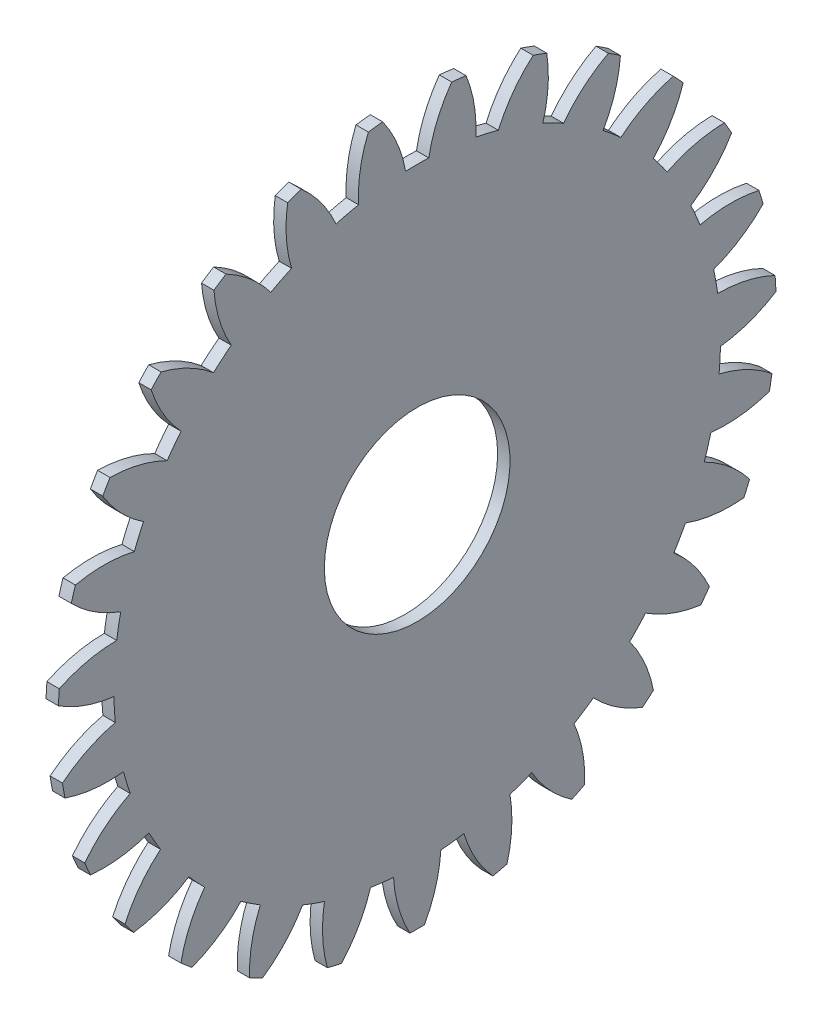
SolidWorks part; units mm, degrees
ref_plane "Plane1" through (0, 0, 0) normal (0, 0, 1) x (1, 0, 0)
ref_plane "Plane2" through (0, 0, 0) normal (0, 1, 0) x (1, 0, 0)
ref_plane "Plane3" through (0, 0, 0) normal (1, 0, 0) x (0, 0, -1)
other "Configuration Table"
sketch "HoldingSke" plane through (0, 0, 0) normal (0, 1, 0) x (1, 0, 0)
  line L0 (0, 0) -> (0.1485, -0.0757)
  line L1 (-15, 0) -> (100, 0) construction
  line L2 (0, 0) -> (-2.1039, 2.3779)
  line L3 (0, 0) -> (-11.863, 4.5341)
  line L4 (0, 0) -> (7.6947, 3.9207)
  line L5 (0, 0) -> (-46.8476, -17.4728)
  line L6 (0, 0) -> (-2.4869, -1.6779)
  line L7 (-2.1039, 2.3779) -> (8.6586, 51.2059)
  line L8 (-76.2, 54.61) -> (-72.4, 54.61)
  line L9 (-71.009, 38.7566) -> (-53.1078, 45.2721)
  line L10 (-76.2, 71.12) -> (104.1128, 71.12)
  line L11 (0, 0) -> (-3, 0)
  line L12 (-76.2, 101.6) -> (-75.993, 101.6)
  line L13 (24.9733, 27.94) -> (52.9518, 28.4284)
  line L14 (24.9733, 27.94) -> (24.9743, 27.94)
  line L15 (24.9733, 27.94) -> (100.4006, 29.5858)
  line L16 (-63.627, -6) -> (-12.827, -6)
  circle A0 centre (0, 0) radius 22.5
  circle A1 centre (0, 0) radius 37.5
  circle A2 centre (0, 0) radius 37.5
  circle A3 centre (0, 0) radius 22.5
  dimension "MHD" = 75
  dimension "Hub_dia" = 75
  dimension "Bore" = 45
  dimension "MBD" = 45
  dimension "Num_teeth" = 27
  dimension "Pitch" = 0.1667
  dimension "Overall_len" = 50
  dimension "Show_teeth" = 27
  dimension "Thickness" = 3
  dimension "OAL" = 50.0001
  dimension "T_dim" = 3.8
  dimension "Ap" = 20
  dimension "H" = 19.05
  dimension "Pitch_radius" = 180.3128
  dimension "Width" = 3
  dimension "Backlash" = 0.207
  dimension "Addendum_fac" = 1
  dimension "Dedendum_fac" = 1.25
  dimension "Clearance_fac" = 0.25
  dimension "Dedendum_add" = 0.001
  dimension "Module" = 6
sketch "BasProSke" plane through (0, 0, 0) normal (0, 1, 0) x (1, 0, 0)
  line L0 (-10, 0) -> (60, 0) construction
  line L1 (0, 0) -> (0, 87)
  line L2 (0, 0) -> (3, 0)
  line L3 (3, 0) -> (3, 87)
  line L4 (3, 87) -> (0, 87)
  dimension "Thickness" = 3
  dimension "Diameter" = 174
revolve "Base-Revolve" add sketch "BasProSke" angle 360 about L0
sketch "TooCutSke" plane through (0, 0, 0) normal (1, 0, 0) x (0, 0, -1)
  line L1 (0, 0) -> (0, 107) construction
  line L2 (0, 0) -> (-5.0719, 80.8411) construction
  line L3 (0, 0) -> (-18.7799, 160.6727) construction
  line L4 (-5.0719, 80.8411) -> (-9.39, 80.3363) construction
  arc A0 (2.8118, 73.4452) -> (-2.8118, 73.4452) centre (0, 0) ccw
  arc A1 (8.3748, 86.6215) -> (-8.3748, 86.6215) centre (0, 0) ccw
  circle A2 centre (0, 0) radius 81 construction
  circle A3 centre (0, 0) radius 76.1151 construction
  arc A4 (-2.8118, 73.4452) -> (-8.3748, 86.6215) centre (-34.706, 67.7422) ccw
  arc A5 (8.3748, 86.6215) -> (2.8118, 73.4452) centre (34.706, 67.7422) ccw
  dimension "Root_dia" = 146.998
  dimension "Overcut_dia" = 174.0508
  dimension "Pitch_dia" = 162
  dimension "Base_dia" = 152.2302
  dimension "Flank_rad" = 32.4
  dimension "Half_ang" = 6.667
  dimension "Half_CT" = 4.3475
extrude "ToothCut" cut sketch "TooCutSke" along normal through all
fillet "Breaks" [suppressed] radius 0.12
fillet "RootFillets" [suppressed] radius 1.501
pattern_circular "TeethCuts" count 27 every 13.333 about axis through (-10, 0, 0) along (1, 0, 0) of "ToothCut", "RootFillets", "Breaks"
sketch "HubNeaOneSke" plane through (0, 0, 0) normal (-1, 0, 0) x (0, 0, 1)
  circle A0 centre (0, 0) radius 37.5
  dimension "Diameter" = 75
extrude "HubNearOne" [suppressed] add sketch "HubNeaOneSke" along normal blind 47.0001
sketch "HubNeaBotSke" plane through (0, 0, 0) normal (-1, 0, 0) x (0, 0, 1)
  circle A0 centre (0, 0) radius 37.5
  dimension "Diameter" = 75
extrude "HubNearBoth" [suppressed] add sketch "HubNeaBotSke" along normal blind 23.5
ref_plane "FarPln" through (3, 0, 0) normal (1, 0, 0) x (0, 0, -1)
sketch "HubFarSke" plane through (3, 0, 0) normal (1, 0, 0) x (0, 0, -1)
  circle A0 centre (0, 0) radius 37.5
  dimension "Diameter" = 75
extrude "HubFar" [suppressed] add sketch "HubFarSke" along normal blind 23.5
sketch "BorSke" plane through (0, 0, 0) normal (1, 0, 0) x (0, 0, -1)
  circle A0 centre (0, 0) radius 22.5
  dimension "Diameter" = 45
extrude "Bore" cut sketch "BorSke" along normal mid plane 100.0001
sketch "KeySke" plane through (0, 0, 0) normal (1, 0, 0) x (0, 0, -1)
  line L0 (-7, 0) -> (-7, 26.3)
  line L1 (-7, 26.3) -> (7, 26.3)
  line L2 (7, 26.3) -> (7, 0)
  line L3 (0, 0) -> (0, 34) construction
  line L4 (-7, 0) -> (7, 0)
  dimension "Offset" = 26.3
  dimension "Width" = 14
extrude "Keyway" [suppressed] cut sketch "KeySke" along normal mid plane 100.0001
pattern_circular "Keyway2" [suppressed] count 2 every 90 about axis through (-10, 0, 0) along (1, 0, 0)
sketch "Sketch1" plane through (3, 0, 0) normal (1, 0, 0) x (0, 0, -1)
  circle A0 centre (0, 0) radius 81.1117
equation "' \"Module@HoldingSke\" = 6.35"
equation "' \"Num_teeth@HoldingSke\" = 12"
equation "' \"Ap@HoldingSke\" =  20"
equation "' \"Ap@HoldingSke\" = 20"
equation "' \"Width@HoldingSke\" = 0.5 * 25.4"
equation "' \"Hub_dia@HoldingSke\"= 1 * 25.4"
equation "' \"Hub_dia@HoldingSke\" = 1 * 25.4"
equation "' \"Overall_len@HoldingSke\" = 1.0 * 25.4"
equation "' \"Bore@HoldingSke\" = 0.75 * 25.4"
equation "' \"T_dim@HoldingSke\" = 0.1 * 25.4"
equation "' \"Width@KeySke\" = 0.25 * 25.4"
equation "' \"Show_teeth@HoldingSke\" = 13"
equation "' \"Backlash@HoldingSke\" = 0.009 * 25.4"
equation "' \"Addendum_fac@HoldingSke\" = 1.0"
equation "' \"Dedendum_fac@HoldingSke\" = 1.25"
equation "' \"Dedendum_add@HoldingSke\" = 0.00005 * 25.4"
equation "' \"Clearance_fac@HoldingSke\" = 0.25"
equation "\"Pitch@HoldingSke\" = 1 / \"Module@HoldingSke\""
equation "\"Overcut_dia@TooCutSke\" = (\"Num_teeth@HoldingSke\" + 2 * \"Addendum_fac@HoldingSke\") / \"Pitch@HoldingSke\" + 0.002 * 25.4"
equation "\"Pitch_dia@TooCutSke\" = \"Num_teeth@HoldingSke\" / \"Pitch@HoldingSke\""
equation "\"Base_dia@TooCutSke\" = \"Num_teeth@HoldingSke\" / \"Pitch@HoldingSke\" * cos((\"Ap@HoldingSke\"  * 3.14159265 / 180))"
equation "\"Root_dia@TooCutSke\" = (\"Num_teeth@HoldingSke\" + 2) / \"Pitch@HoldingSke\" - 2 * (\"Addendum_fac@HoldingSke\" + \"Dedendum_fac@HoldingSke\") / \"Pitch@HoldingSke\" - \"Dedendum_add@HoldingSke\" * 2"
equation "\"Half_ang@TooCutSke\" = 180 / \"Num_teeth@HoldingSke\""
equation "\"Half_CT@TooCutSke\" = \"Num_teeth@HoldingSke\" / \"Pitch@HoldingSke\" * sin((3.14159265 / 2 / \"Num_teeth@HoldingSke\")) / 2 - 7 * \"Backlash@HoldingSke\" / 4"
equation "\"Flank_rad@TooCutSke\" = \"Num_teeth@HoldingSke\" / \"Pitch@HoldingSke\" / 5"
equation "\"Radius@RootFillets\" = \"Clearance_fac@HoldingSke\" / \"Pitch@HoldingSke\" + \"Dedendum_add@HoldingSke\""
equation "\"Break_rad@Breaks\" = 0.02 / \"Pitch@HoldingSke\""
equation "\"Thickness@HoldingSke\" = \"Width@HoldingSke\""
equation "\"OAL@HoldingSke\" = \"Thickness@HoldingSke\""
equation "\"MHD@HoldingSke\" = (\"Num_teeth@HoldingSke\" + 2) / \"Pitch@HoldingSke\" - 2 * (\"Addendum_fac@HoldingSke\" + \"Dedendum_fac@HoldingSke\")  / \"Pitch@HoldingSke\" - \"Dedendum_add@HoldingSke\" * 2"
equation "\"MBD@HoldingSke\" = (\"Num_teeth@HoldingSke\" + 2) / \"Pitch@HoldingSke\" - 2 * (\"Addendum_fac@HoldingSke\" + \"Dedendum_fac@HoldingSke\")  / \"Pitch@HoldingSke\" - \"Dedendum_add@HoldingSke\" * 2 - 0.002 * 25.4"
equation "\"MHD@HoldingSke\" = ((sgn( \"MHD@HoldingSke\" - \"Hub_dia@HoldingSke\" )-1)*( \"MHD@HoldingSke\" - \"Hub_dia@HoldingSke\" ))/-2+ \"Hub_dia@HoldingSke\""
equation "\"MBD@HoldingSke\" = ((sgn( \"MBD@HoldingSke\" - \"Bore@HoldingSke\" )-1)*( \"MBD@HoldingSke\" - \"Bore@HoldingSke\" ))/-2+ \"Bore@HoldingSke\""
equation "\"OAL@HoldingSke\" = ((sgn( \"OAL@HoldingSke\" - \"Overall_len@HoldingSke\" )+1)*( \"OAL@HoldingSke\" - \"Overall_len@HoldingSke\" ))/2 + \"Overall_len@HoldingSke\" + 0.000002 * 25.4"
equation "\"Num_teeth@TeethCuts\" = int( \"Show_teeth@HoldingSke\" ) + 1"
equation "\"Num_teeth@TeethCuts\" = ((sgn( \"Num_teeth@TeethCuts\" - \"Num_teeth@HoldingSke\" )-1)*( \"Num_teeth@TeethCuts\" - \"Num_teeth@HoldingSke\" ))/-2+ \"Num_teeth@HoldingSke\""
equation "\"Num_teeth@TeethCuts\" = ((sgn( \"Num_teeth@TeethCuts\" - 2.0)+1)*( \"Num_teeth@TeethCuts\" - 2.0))/2 +2.0"
equation "\"Angle@TeethCuts\" = 360.0 / \"Num_teeth@HoldingSke\""
equation "\"Diameter@BasProSke\" = (\"Num_teeth@HoldingSke\" + 2 * \"Addendum_fac@HoldingSke\") / \"Pitch@HoldingSke\""
equation "\"Thickness@BasProSke\"  = \"Thickness@HoldingSke\""
equation "' \"Fillet_rad@BasProSke\" =  \"Thickness@HoldingSke\" * 0.05"
equation "' \"Fillet_rad@BasProSke\" = \"Thickness@HoldingSke\" * 0.05"
equation "\"MHD@HoldingSke\" = ((sgn( \"MHD@HoldingSke\" - \"Root_dia@TooCutSke\" )-1)*( \"MHD@HoldingSke\" - \"Root_dia@TooCutSke\" ))/-2+ \"Root_dia@TooCutSke\""
equation "\"Diameter@HubNeaOneSke\" = \"MHD@HoldingSke\""
equation "\"Length@HubNearOne\" = \"OAL@HoldingSke\" - \"Thickness@BasProSke\""
equation "\"Diameter@HubNeaBotSke\" = \"MHD@HoldingSke\""
equation "\"Length@HubNearBoth\" = ( \"OAL@HoldingSke\" - \"Thickness@BasProSke\" ) / 2.0"
equation "\"Thickness@FarPln\" = \"Thickness@BasProSke\""
equation "\"Diameter@HubFarSke\" = \"MHD@HoldingSke\""
equation "\"Length@HubFar\" = ( \"OAL@HoldingSke\" - \"Thickness@BasProSke\" ) / 2.0"
equation "\"Diameter@BorSke\" = \"MBD@HoldingSke\""
equation "\"D1@Bore\" = \"OAL@HoldingSke\" * 2.0"
equation "\"D1@Keyway\" = \"OAL@HoldingSke\" * 2.0"
equation "\"Offset@KeySke\" = \"T_dim@HoldingSke\" + \"MBD@HoldingSke\" / 2.0"
